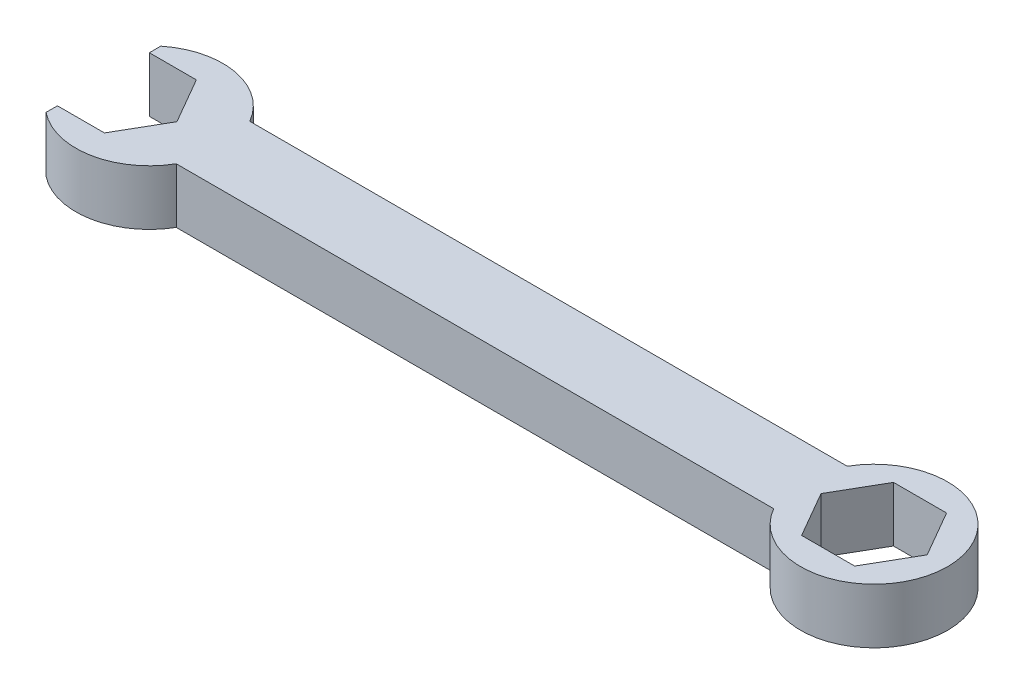
SolidWorks part; units mm, degrees
ref_plane "Front Plane" through (0, 0, 0) normal (0, 0, 1) x (1, 0, 0)
ref_plane "Top Plane" through (0, 0, 0) normal (0, 1, 0) x (1, 0, 0)
ref_plane "Right Plane" through (0, 0, 0) normal (1, 0, 0) x (0, 0, -1)
sketch "Sketch1" plane through (0, 0, 0) normal (0, 1, 0) x (1, 0, 0)
  line L0 (0, 0) -> (-100.1476, 0) construction
  line L1 (7.3323, 0) -> (3.6662, 6.35)
  line L2 (3.6662, 6.35) -> (-3.6662, 6.35)
  line L3 (-3.6662, 6.35) -> (-7.3323, 0)
  line L4 (-7.3323, 0) -> (-3.6662, -6.35)
  line L5 (-3.6662, -6.35) -> (3.6662, -6.35)
  line L6 (3.6662, -6.35) -> (7.3323, 0)
  line L7 (-91.3488, 5.08) -> (-8.7988, 5.08)
  line L8 (-91.3488, -5.08) -> (-8.7988, -5.08)
  line L9 (-106.4976, 7.9311) -> (-106.4976, -7.9311)
  line L17 (-96.3376, 0) -> (-100.0038, 6.35)
  line L18 (-100.0038, 6.35) -> (-107.3362, 6.35)
  line L19 (-107.3362, 6.35) -> (-111.0023, 0)
  line L20 (-111.0023, 0) -> (-107.3362, -6.35)
  line L21 (-107.3362, -6.35) -> (-100.0038, -6.35)
  line L22 (-100.0038, -6.35) -> (-96.3376, 0)
  circle A0 centre (0, 0) radius 6.35 construction
  circle A1 centre (0, 0) radius 10.16
  circle A2 centre (-100.1476, 0) radius 10.16
  circle A3 centre (-103.67, 0) radius 6.35 construction
  point P25 (0, 0)
  dimension "D2" = 20.32
  dimension "D3" = 20.32
  dimension "D1" = 12.7
  dimension "D4" = 5.08
  dimension "D5" = 5.08
  dimension "D6" = 82.55
  dimension "D7" = 12.7
  dimension "D8" = 6.35
  dimension "D9" = 10.16
extrude "Boss-Extrude1" add sketch "Sketch1" along normal blind 7.62 contours A1 L6 L5 L4 L3 L2 L1 | A2 L8 A1 L7 | A2 L9 L18 L17 L22 L21
